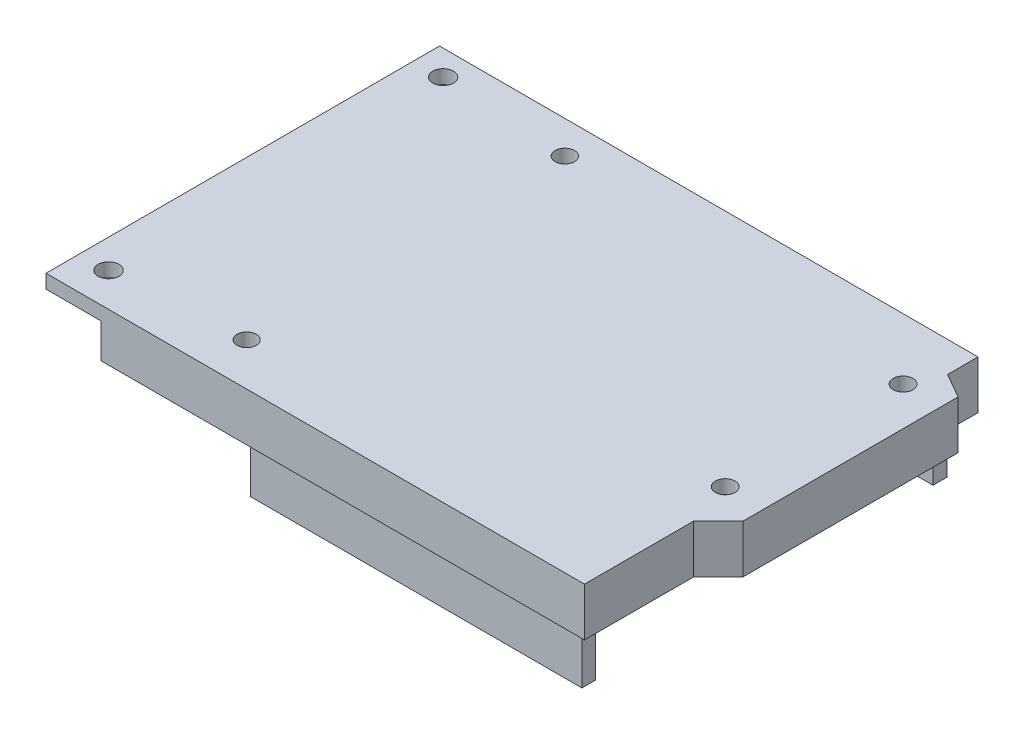
SolidWorks part; units mm, degrees
ref_plane "前视基准面" through (0, 0, 0) normal (0, 0, 1) x (1, 0, 0)
ref_plane "上视基准面" through (0, 0, 0) normal (0, 1, 0) x (1, 0, 0)
ref_plane "右视基准面" through (0, 0, 0) normal (1, 0, 0) x (0, 0, -1)
sketch "草图1" plane through (0, 0, 0) normal (0, 1, 0) x (1, 0, 0)
  line L0 (0, 15.8132) -> (3.5789, 19.3921)
  line L1 (0, 0) -> (-78, 0)
  line L2 (0, 0) -> (0, 15.8132)
  line L3 (0, 57) -> (-78, 57)
  line L4 (-78, 0) -> (-78, 57)
  line L5 (3.5789, 19.3921) -> (3.5789, 50.5492)
  line L6 (3.5789, 50.5492) -> (0, 52.5983)
  line L7 (0, 52.5983) -> (0, 57)
  circle A0 centre (-73.457, 52.5983) radius 2.7383
  circle A1 centre (-73.5509, 3.4806) radius 2.7
  circle A2 centre (-56.5616, 52.5983) radius 2.5232
  circle A3 centre (-56.5616, 3.4806) radius 2.5232
  circle A4 centre (-2.26, 48.0069) radius 1.8255
  circle A5 centre (-2.26, 23.2987) radius 1.8156
  point P21 (0, 0)
  dimension "D1" = 78
  dimension "D2" = 57
extrude "凸台-拉伸1" add sketch "草图1" along normal blind 7 contours L1 L4 L3 L7 L6 L5 L0 L2
sketch "草图2" plane through (0, 7, 0) normal (0, 1, 0) x (1, 0, 0)
  circle A0 centre (-73.8394, 53.3623) radius 1.4991
  circle A1 centre (-73.8394, 4.8945) radius 1.5077
extrude "切除-拉伸1" cut sketch "草图2" against normal blind 2
sketch "草图3" plane through (0, 7, 0) normal (0, 1, 0) x (1, 0, 0)
  circle A0 centre (-55.117, 52.2702) radius 1.4042
  circle A1 centre (-55.117, 6.1808) radius 1.3947
  circle A2 centre (-2.024, 48.1673) radius 1.4262
  circle A3 centre (-2.024, 22.4057) radius 1.43
extrude "切除-拉伸2" cut sketch "草图3" against normal blind 2
sketch "草图5" plane through (0, 0, 0) normal (0, 0, 1) x (1, 0, 0)
  line L1 (-78, 0) -> (-70, 0)
  line L2 (-78, 0) -> (-78, 5)
  line L3 (-78, 5) -> (-70, 5)
  line L4 (-70, 0) -> (-70, 5)
  dimension "D1" = 8
  dimension "D2" = 5
extrude "切除-拉伸3" cut sketch "草图5" against normal blind 135 contours L2 L1 L4 L3
sketch "草图6" plane through (0, 0, 0) normal (0, -1, 0) x (-1, 0, 0)
  line L1 (2.6607, 2.2865) -> (50.6607, 2.2865)
  line L2 (2.6607, 2.2865) -> (2.6607, 4.2865)
  line L3 (2.6607, 4.2865) -> (50.6607, 4.2865)
  line L4 (50.6607, 2.2865) -> (50.6607, 4.2865)
  line L5 (2.6607, 55.142) -> (41.1607, 55.142)
  line L6 (2.6607, 55.142) -> (2.6607, 53.142)
  line L7 (2.6607, 53.142) -> (41.1607, 53.142)
  line L8 (41.1607, 55.142) -> (41.1607, 53.142)
  point P8 (0, 0)
  dimension "D1" = 48
  dimension "D2" = 2
  dimension "D3" = 38.5
  dimension "D4" = 2
extrude "凸台-拉伸2" add sketch "草图6" along normal blind 8.5
sketch "草图7" plane through (0, 0, 0) normal (0, -1, 0) x (-1, 0, 0)
  line L1 (59.2514, 12.2959) -> (75.2514, 12.2959)
  line L2 (59.2514, 12.2959) -> (59.2514, 23.7959)
  line L3 (59.2514, 23.7959) -> (75.2514, 23.7959)
  line L4 (75.2514, 12.2959) -> (75.2514, 23.7959)
  dimension "D1" = 11.5
  dimension "D2" = 16
extrude "凸台-拉伸3" add sketch "草图7" along normal blind 10 contours L2 L1 L4 L3
sketch "草图9" plane through (-41.1607, 0, 0) normal (-1, 0, 0) x (0, 0, 1)
  line L0 (-53.142, -8.5) -> (-55.142, -8.5) construction
  line L1 (-55.142, 0) -> (-53.142, 0)
  line L2 (-55.142, 0) -> (-55.142, -8.5)
  line L3 (-55.142, -8.5) -> (-53.142, -8.5)
  line L4 (-53.142, 0) -> (-53.142, -8.5)
  line L5 (-53.142, -8.5) -> (-53.142, 0) construction
extrude "切除-拉伸4" cut sketch "草图9" against normal blind 10
sketch "草图10" plane through (-70, 0, 0) normal (-1, 0, 0) x (0, 0, 1)
  line L0 (-23.7959, 0) -> (-57, 0) construction
  line L1 (-54.3372, 0) -> (-45.3372, 0)
  line L2 (-54.3372, 0) -> (-54.3372, -11)
  line L3 (-54.3372, -11) -> (-45.3372, -11)
  line L4 (-45.3372, 0) -> (-45.3372, -11)
  dimension "D1" = 11
  dimension "D2" = 9
extrude "凸台-拉伸4" add sketch "草图10" against normal blind 3 separate body
sketch "草图11" plane through (-67, 0, 0) normal (1, 0, 0) x (0, 0, -1)
  line L0 (54.3372, 0) -> (54.3372, -11) construction
  line L1 (45.3372, 0) -> (54.3372, 0)
  line L2 (45.3372, 0) -> (45.3372, -6.5)
  line L4 (54.3372, 0) -> (54.3372, -6.5)
  arc A0 (45.3372, -6.5) -> (54.3372, -6.5) centre (49.8372, -6.5) ccw
  dimension "D1" = 6.5
extrude "凸台-拉伸5" add sketch "草图11" along normal blind 10.5
sketch "草图12" plane through (0, 5, 0) normal (0, 1, 0) x (1, 0, 0)
  circle A1 centre (-55.117, 52.2702) radius 1.4042
  circle A2 centre (-55.117, 6.1808) radius 1.3947
  circle A3 centre (-2.0406, 22.42) radius 1.452
  circle A4 centre (-2.024, 48.1673) radius 1.4262
extrude "切除-拉伸5" cut sketch "草图12" against normal blind 10.5
